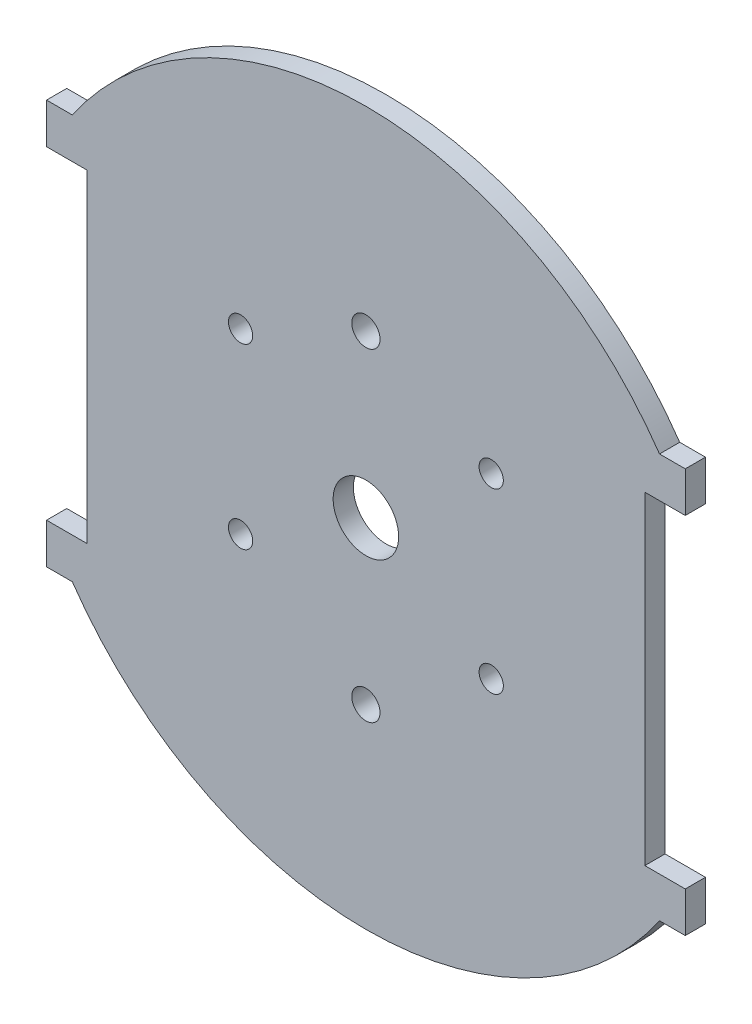
SolidWorks part; units mm, degrees
ref_plane "Alzado" through (0, 0, 0) normal (0, 0, 1) x (1, 0, 0)
ref_plane "Planta" through (0, 0, 0) normal (0, 1, 0) x (1, 0, 0)
ref_plane "Vista lateral" through (0, 0, 0) normal (1, 0, 0) x (0, 0, -1)
sketch "Croquis1" plane through (0, 0, 0) normal (0, 0, 1) x (1, 0, 0)
  line L0 (-34.5003, 20) -> (-22.2908, 20) construction
  line L1 (-39.5003, 20) -> (-34.5003, 20)
  line L2 (-34.5003, 20) -> (-34.5003, -20)
  line L3 (-22.2908, -20) -> (-34.5003, -20) construction
  line L4 (-34.5003, 20) -> (-34.5003, 11.75) construction
  line L5 (36.317, -25) -> (39.5003, -25)
  line L6 (36.317, 25) -> (39.5003, 25)
  line L7 (-39.5003, -20) -> (-34.5003, -20)
  line L8 (-39.5003, 20) -> (-39.5003, 25)
  line L9 (39.5003, 20) -> (34.5003, 20)
  line L10 (-39.5003, 25) -> (-36.317, 25)
  line L11 (39.5003, -20) -> (34.5003, -20)
  line L12 (34.5003, 20) -> (34.5003, -20)
  line L13 (39.5003, 20) -> (39.5003, 25)
  line L14 (-39.5003, -25) -> (-36.317, -25)
  line L15 (-39.5003, -20) -> (-39.5003, -25)
  line L17 (39.5003, -20) -> (39.5003, -25)
  arc A0 (-36.317, -25) -> (36.317, -25) centre (0, 0) ccw
  arc A1 (36.317, 25) -> (-36.317, 25) centre (0, 0) ccw
  circle A2 centre (0, 0) radius 4.05
  circle A3 centre (0, 20) radius 1.75
  circle A4 centre (0, -20) radius 1.75
  dimension "D1" = 40
  dimension "D2" = 20
  dimension "D5" = 40
  dimension "D6" = 44.09
  dimension "D3" = 3.1833
  dimension "D4" = 3.1833
  dimension "D7" = 5
  dimension "D8" = 5
  dimension "D9" = 3.1833
  dimension "D10" = 5
  dimension "D11" = 5
  dimension "D12" = 3.1833
  dimension "D13" = 5
  dimension "D14" = 5
  dimension "D15" = 5
  dimension "D16" = 5
  dimension "D17" = 20
  dimension "D18" = 40
  dimension "D19" = 34.5003
  dimension "D20" = 69.0007
extrude "Saliente-Extruir1" add sketch "Croquis1" along normal blind 2.5
sketch "Croquis2" plane through (0, 0, 0) normal (0, 0, -1) x (-1, 0, 0)
  circle A0 centre (15.5, -9.5) radius 1.5
  circle A1 centre (15.5, 12.5) radius 1.5
  circle A2 centre (-15.5, 12.5) radius 1.5
  circle A3 centre (-15.5, -9.5) radius 1.5
extrude "Cortar-Extruir1" cut sketch "Croquis2" against normal blind 4
